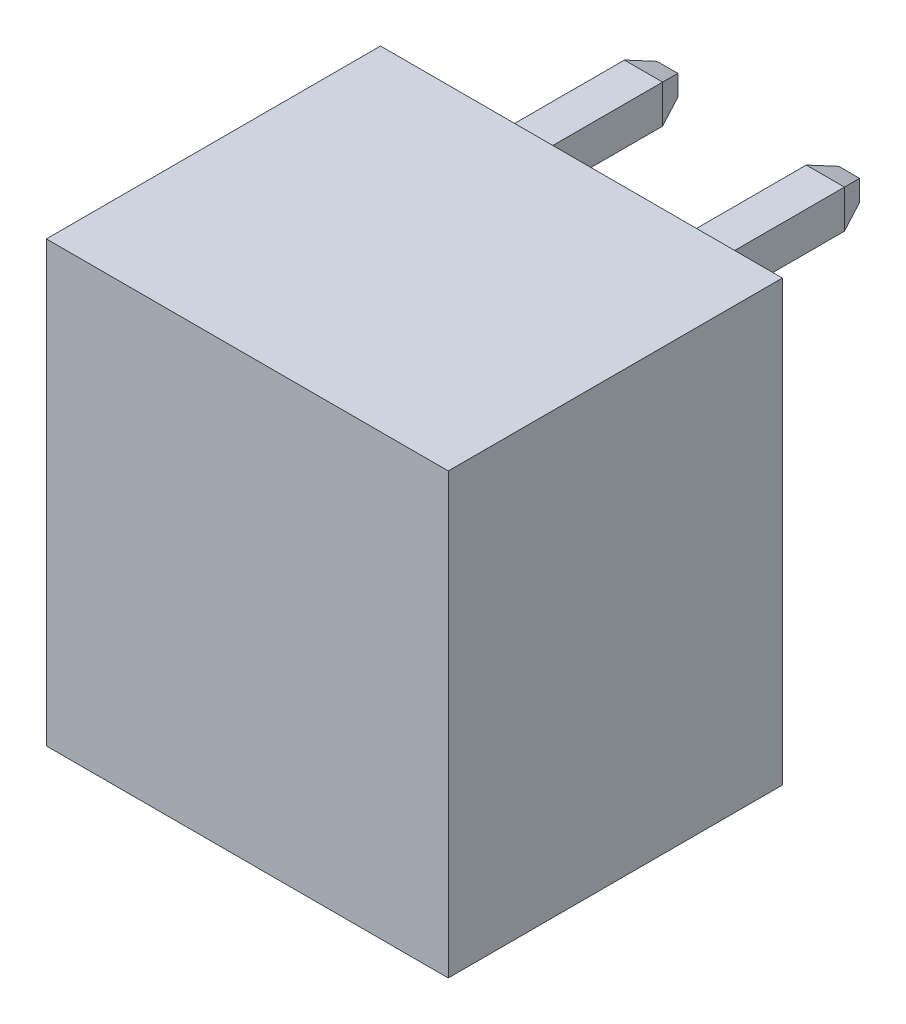
SolidWorks part; units mm, degrees
ref_plane "Front Plane" through (0, 0, 0) normal (0, 0, 1) x (1, 0, 0)
ref_plane "Top Plane" through (0, 0, 0) normal (0, 1, 0) x (1, 0, 0)
ref_plane "Right Plane" through (0, 0, 0) normal (1, 0, 0) x (0, 0, -1)
sketch "Sketch1" plane through (0, 0, 0) normal (0, 0, 1) x (1, 0, 0)
  line L1 (-4.21, 4.6) -> (4.21, 4.6)
  line L2 (-4.21, 4.6) -> (-4.21, -4.6)
  line L3 (-4.21, -4.6) -> (4.21, -4.6)
  line L4 (4.21, 4.6) -> (4.21, -4.6)
  line L5 (-4.21, 4.6) -> (4.21, -4.6) construction
  line L6 (-4.21, -4.6) -> (4.21, 4.6) construction
  point P0 (0, 0)
  dimension "D1" = 9.2
  dimension "D2" = 8.42
extrude "Boss-Extrude1" add sketch "Sketch1" along normal blind 7
sketch "Sketch2" plane through (0, -4.6, 0) normal (0, -1, 0) x (1, 0, 0)
  line L0 (-3.535, 5.11) -> (-2.705, 5.11)
  line L1 (-0.275, 5.11) -> (-1.105, 5.11)
  line L2 (-3.535, 5.11) -> (-3.535, 0.66)
  line L3 (-3.535, 0.66) -> (-2.845, 0.66)
  line L4 (-0.275, 5.11) -> (-0.275, 0.66)
  line L5 (-2.705, 5.11) -> (-2.705, 5.79)
  line L6 (-1.105, 5.11) -> (-1.105, 5.79)
  line L7 (-2.705, 5.79) -> (-3.205, 5.79)
  line L8 (-1.105, 5.79) -> (-0.605, 5.79)
  line L9 (-3.205, 5.79) -> (-3.3538, 6.34)
  line L10 (-0.605, 5.79) -> (-0.4562, 6.34)
  line L11 (-3.3538, 6.34) -> (-0.4562, 6.34)
  line L12 (-0.275, 0.66) -> (-0.965, 0.66)
  line L13 (-3.535, 0.904) -> (-0.275, 0.904) construction
  line L14 (-3.3538, 6.34) -> (-3.3538, 0.66) construction
  line L15 (-4.21, 7) -> (4.21, 7) construction
  line L16 (-4.21, 0) -> (-4.21, 7) construction
  arc A0 (-2.845, 0.66) -> (-0.965, 0.66) centre (-1.905, -1.0287) cw
  point P17 (-4.21, 3.5)
  point P19 (-3.3538, 3.5)
  dimension "D9" = 0.244
  dimension "D1" = 3.26
  dimension "D2" = 4.45
  dimension "D3" = 0.83
  dimension "D4" = 0.68
  dimension "D5" = 0.5
  dimension "D6" = 105.14
  dimension "D7" = 0.55
  dimension "D8" = 105.14
  dimension "D10" = 0.69
  dimension "D11" = 0.69
  dimension "D14" = 0.675
extrude "Cut-Extrude1" cut sketch "Sketch2" against normal blind 7
pattern_linear "LPattern1" count 2 spacing 3.81 along (1, 0, 0) of "Cut-Extrude1"
sketch "Sketch3" plane through (0, 2.4, 0) normal (0, -1, 0) x (1, 0, 0)
  line L0 (-3.535, 0.66) -> (-3.535, 2.985) construction
  line L2 (-3.535, 5.11) -> (-3.535, 0.66) construction
  line L4 (-3.535, 2.985) -> (-0.275, 2.985) construction
  line L5 (-0.275, 0.66) -> (-0.275, 5.11) construction
  line L6 (-3.535, 0.66) -> (-2.845, 0.66) construction
  circle A0 centre (-1.905, 2.985) radius 0.875
  dimension "D2" = 1.75
  dimension "D1" = 2.325
extrude "Boss-Extrude2" add sketch "Sketch3" along normal blind 1.15
chamfer "Chamfer1" distance 0.5 angle 6.48 1 edges at (-1.905, 1.25, 2.11)
sketch "Sketch4" plane through (0, 1.25, 0) normal (0, -1, 0) x (1, 0, 0)
  line L1 (-2.31, 3.39) -> (-1.5, 3.39)
  line L2 (-2.31, 3.39) -> (-2.31, 2.58)
  line L3 (-2.31, 2.58) -> (-1.5, 2.58)
  line L4 (-1.5, 3.39) -> (-1.5, 2.58)
  line L5 (-2.31, 3.39) -> (-1.5, 2.58) construction
  line L6 (-2.31, 2.58) -> (-1.5, 3.39) construction
  point P0 (-1.905, 2.985)
  dimension "D1" = 0.81
  dimension "D2" = 0.81
extrude "Boss-Extrude3" add sketch "Sketch4" along normal blind 4.45
chamfer "Chamfer2" distance 0.5 angle 20 4 edges at (-1.905, -3.2, 2.58) (-1.5, -3.2, 2.985) (-2.31, -3.2, 2.985) (-1.905, -3.2, 3.39)
pattern_linear "LPattern3" count 2 spacing 3.81 along (1, 0, 0) of "Chamfer1", "Boss-Extrude2"
pattern_linear "LPattern4" count 2 spacing 3.81 along (1, 0, 0) of "Chamfer2", "Boss-Extrude3"
sketch "Sketch5" plane through (0, 0, 0) normal (0, 0, -1) x (-1, 0, 0)
  line L0 (1.9, 4.6) -> (1.9, 3.3) construction
  line L1 (-4.21, 4.6) -> (4.21, 4.6) construction
  line L3 (4.21, 4.6) -> (4.21, -4.6) construction
  line L6 (2.3, 2.9) -> (1.5, 2.9)
  line L7 (2.3, 2.9) -> (2.3, 3.7)
  line L8 (2.3, 3.7) -> (1.5, 3.7)
  line L9 (1.5, 2.9) -> (1.5, 3.7)
  line L10 (2.3, 2.9) -> (1.5, 3.7) construction
  line L11 (2.3, 3.7) -> (1.5, 2.9) construction
  dimension "D1" = 1.3
  dimension "D2" = 2.31
  dimension "D3" = 0.8
  dimension "D4" = 0.8
extrude "Boss-Extrude4" add sketch "Sketch5" along normal blind 3.7 and the other way blind 3.4 contours L6 L9 L8 L7
chamfer "Chamfer3" distance 0.5 angle 20 4 edges at (-1.9, 2.9, -3.7) (-1.5, 3.3, -3.7) (-1.9, 3.7, -3.7) (-2.3, 3.3, -3.7)
pattern_linear "LPattern12" count 2 spacing 3.81 along (1, 0, 0) of "Chamfer3", "Boss-Extrude4"
equation "\"PIN\"= 2"
equation "\"D2@Sketch1\"=\"PIN\"*3.81+0.8"
equation "\"D1@LPattern1\"=\"PIN\""
equation "\"D1@LPattern4\"=\"PIN\""
equation "\"D1@LPattern3\"=\"PIN\""
equation "\"D1@LPattern12\"=\"PIN\""
